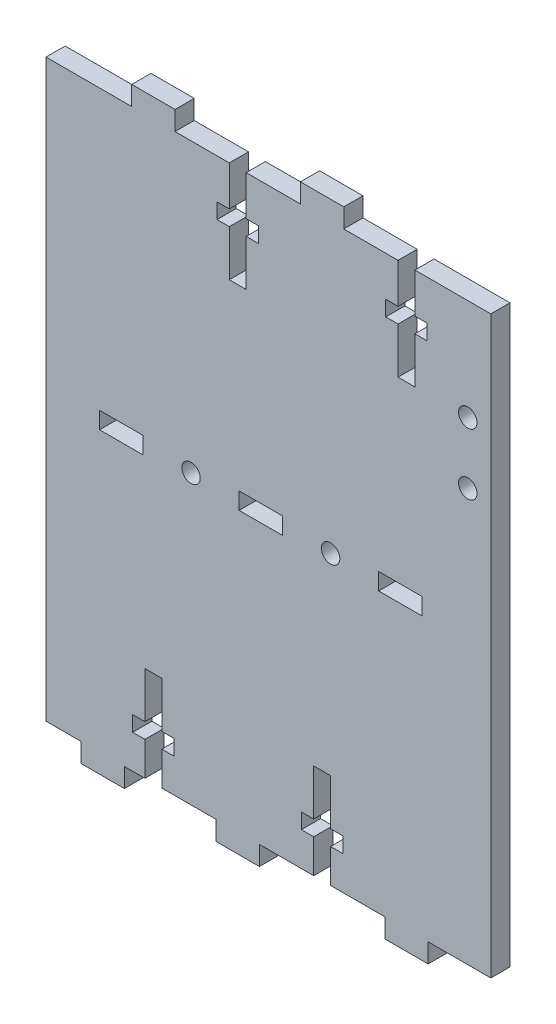
SolidWorks part; units mm, degrees
ref_plane "Front Plane" through (0, 0, 0) normal (0, 0, 1) x (1, 0, 0)
ref_plane "Top Plane" through (0, 0, 0) normal (0, 1, 0) x (1, 0, 0)
ref_plane "Right Plane" through (0, 0, 0) normal (1, 0, 0) x (0, 0, -1)
sketch "Sketch1" plane through (0, 0, 0) normal (0, 0, 1) x (1, 0, 0)
  line L0 (0, 0) -> (69.85, 0)
  line L1 (69.85, 0) -> (69.85, 95.25)
  line L2 (69.85, 95.25) -> (0, 95.25)
  line L3 (0, 95.25) -> (0, 0)
  line L4 (34.925, 95.25) -> (34.925, 0) construction
  line L5 (0, 47.625) -> (69.85, 47.625) construction
  line L6 (13.97, 0) -> (13.97, 15.748)
  line L7 (27.94, 95.25) -> (27.94, 78.486)
  line L8 (41.91, 0) -> (41.91, 15.748)
  line L9 (55.88, 95.25) -> (55.88, 78.486)
  line L10 (12.573, 15.748) -> (15.367, 15.748)
  line L11 (15.367, 15.748) -> (15.367, 8.128)
  line L12 (15.367, 8.128) -> (17.399, 8.128)
  line L13 (17.399, 8.128) -> (17.399, 5.588)
  line L14 (17.399, 5.588) -> (15.367, 5.588)
  line L15 (15.367, 5.588) -> (15.367, 0)
  line L16 (12.573, 5.588) -> (12.573, 0)
  line L17 (10.541, 5.588) -> (12.573, 5.588)
  line L18 (10.541, 8.128) -> (10.541, 5.588)
  line L19 (12.573, 8.128) -> (10.541, 8.128)
  line L20 (12.573, 15.748) -> (12.573, 8.128)
  line L21 (45.339, 5.588) -> (43.307, 5.588)
  line L22 (45.339, 8.128) -> (45.339, 5.588)
  line L23 (43.307, 8.128) -> (45.339, 8.128)
  line L24 (43.307, 15.748) -> (43.307, 8.128)
  line L25 (43.307, 15.748) -> (40.513, 15.748)
  line L26 (40.513, 15.748) -> (40.513, 8.128)
  line L27 (40.513, 8.128) -> (38.481, 8.128)
  line L28 (38.481, 8.128) -> (38.481, 5.588)
  line L29 (38.481, 5.588) -> (40.513, 5.588)
  line L30 (40.513, 5.588) -> (40.513, 0)
  line L31 (43.307, 5.588) -> (43.307, 0)
  line L32 (26.543, 78.486) -> (29.337, 78.486)
  line L33 (29.337, 78.486) -> (29.337, 86.106)
  line L34 (29.337, 86.106) -> (31.369, 86.106)
  line L35 (31.369, 86.106) -> (31.369, 88.646)
  line L36 (31.369, 88.646) -> (29.337, 88.646)
  line L37 (29.337, 88.646) -> (29.337, 95.25)
  line L38 (26.543, 88.646) -> (26.543, 95.25)
  line L39 (24.511, 88.646) -> (26.543, 88.646)
  line L40 (24.511, 86.106) -> (24.511, 88.646)
  line L41 (26.543, 86.106) -> (24.511, 86.106)
  line L42 (26.543, 78.486) -> (26.543, 86.106)
  line L43 (54.483, 88.646) -> (54.483, 95.25)
  line L44 (52.451, 88.646) -> (54.483, 88.646)
  line L45 (52.451, 86.106) -> (52.451, 88.646)
  line L46 (54.483, 86.106) -> (52.451, 86.106)
  line L47 (54.483, 78.486) -> (54.483, 86.106)
  line L48 (57.277, 78.486) -> (54.483, 78.486)
  line L49 (57.277, 78.486) -> (57.277, 86.106)
  line L50 (57.277, 86.106) -> (59.309, 86.106)
  line L51 (59.309, 86.106) -> (59.309, 88.646)
  line L52 (59.309, 88.646) -> (57.277, 88.646)
  line L53 (57.277, 88.646) -> (57.277, 95.25)
  line L54 (2.0002, 0) -> (2.0002, -3.175)
  line L55 (2.0002, -3.175) -> (9.1757, -3.175)
  line L56 (9.1757, -3.175) -> (9.1757, 0)
  line L57 (5.588, -3.175) -> (5.588, 0)
  line L58 (13.97, 95.25) -> (13.97, 98.425)
  line L59 (10.3823, 98.425) -> (17.5578, 98.425)
  line L60 (17.5578, 98.425) -> (17.5578, 95.25)
  line L61 (10.3823, 98.425) -> (10.3823, 95.25)
  line L62 (38.3222, 98.425) -> (38.3222, 95.25)
  line L63 (45.4977, 98.425) -> (38.3222, 98.425)
  line L64 (45.4977, 98.425) -> (45.4977, 95.25)
  line L65 (27.94, 0) -> (27.94, -3.175)
  line L66 (24.3523, -3.175) -> (31.5278, -3.175)
  line L67 (31.5278, -3.175) -> (31.5278, 0)
  line L68 (24.3523, -3.175) -> (24.3523, 0)
  line L69 (52.2923, -3.175) -> (52.2923, 0)
  line L70 (59.4678, -3.175) -> (52.2923, -3.175)
  line L71 (59.4678, -3.175) -> (59.4678, 0)
  line L73 (0, 95.25) -> (-3.81, 95.25)
  line L74 (0, 95.25) -> (0, 0)
  line L75 (0, 0) -> (-3.81, 0)
  line L76 (-3.81, 95.25) -> (-3.81, 0)
  dimension "D1" = 69.85
  dimension "D2" = 95.25
  dimension "D3" = 13.97
  dimension "D4" = 27.94
  dimension "D5" = 15.748
  dimension "D6" = 15.748
  dimension "D7" = 13.97
  dimension "D8" = 16.764
  dimension "D9" = 13.97
  dimension "D10" = 1.397
  dimension "D11" = 6.858
  dimension "D12" = 2.54
  dimension "D13" = 1.397
  dimension "D14" = 1.397
  dimension "D15" = 7.62
  dimension "D16" = 2.54
  dimension "D17" = 6.858
  dimension "D18" = 2.794
  dimension "D19" = 7.62
  dimension "D20" = 16.764
  dimension "D21" = 5.588
  dimension "D22" = 3.175
  dimension "D23" = 7.1755
  dimension "D24" = 3.175
  dimension "D25" = 3.5877
  dimension "D26" = 3.5877
  dimension "D27" = 3.175
  dimension "D28" = 3.81
  dimension "D29" = 6.604
  dimension "D30" = 2.032
  dimension "D31" = 3.81
extrude "Boss-Extrude1" add sketch "Sketch1" along normal blind 3.175 contours L53 L52 L51 L50 L49 L48 L47 L46 L45 L44 L43 L2 L37 L36 L35 L34 L33 L32 L42 L41 L40 L39 L38 L3 L0 L16 L17 L18 L19 L20 L10 L11 L12 L13 L14 L15 | L59 L61 L2 L58 | L60 L59 L58 L2 | L64 L63 L62 L2 | L70 L71 L0 L69 | L57 L55 L56 L0 | L55 L57 L0 L54 | L68 L66 L65 L0 | L66 L67 L0 L65 | L73 L76 L75 L3
sketch "Sketch4" plane through (0, 0, 3.175) normal (0, 0, 1) x (1, 0, 0)
  line L0 (66.04, 68.326) -> (66.04, 78.486)
  line L1 (69.85, 0) -> (69.85, 95.25) construction
  line L3 (69.85, 69.85) -> (69.85, 0)
  line L8 (69.85, 59.69) -> (69.85, 0)
  circle A4 centre (66.04, 68.326) radius 1.524
  circle A5 centre (66.04, 78.486) radius 1.524
  dimension "D2" = 10.16
extrude "Cut-Extrude1" cut sketch "Sketch4" against normal through all
sketch "Sketch5" plane through (0, 0, 3.175) normal (0, 0, 1) x (1, 0, 0)
  line L0 (-3.81, 0) -> (-3.81, 47.625)
  line L1 (-3.81, 95.25) -> (-3.81, 0) construction
  line L2 (-3.81, 47.625) -> (5.0615, 47.625)
  line L3 (5.0615, 47.625) -> (5.0615, 49.022)
  line L4 (5.0615, 47.625) -> (5.0615, 46.228)
  line L5 (5.0615, 46.228) -> (12.237, 46.228)
  line L6 (12.237, 46.228) -> (12.237, 49.022)
  line L7 (12.237, 49.022) -> (5.0615, 49.022)
  line L8 (12.237, 47.625) -> (20.2063, 47.625)
  line L9 (20.2063, 47.625) -> (28.1755, 47.625)
  line L10 (28.1755, 47.625) -> (28.1755, 49.022)
  line L11 (28.1755, 49.022) -> (35.351, 49.022)
  line L12 (35.351, 49.022) -> (35.351, 46.228)
  line L13 (35.351, 46.228) -> (28.1755, 46.228)
  line L14 (28.1755, 46.228) -> (28.1755, 47.625)
  line L15 (28.1755, 46.228) -> (28.1755, 47.625)
  line L16 (35.351, 47.625) -> (43.3203, 47.625)
  line L17 (43.3203, 47.625) -> (51.2895, 47.625)
  line L18 (51.2895, 47.625) -> (51.2895, 49.022)
  line L19 (51.2895, 49.022) -> (58.465, 49.022)
  line L20 (58.465, 49.022) -> (58.465, 46.228)
  line L21 (58.465, 46.228) -> (51.2895, 46.228)
  line L22 (51.2895, 46.228) -> (51.2895, 47.625)
  circle A0 centre (20.2063, 47.625) radius 1.524
  circle A1 centre (43.3203, 47.625) radius 1.524
  dimension "D6" = 7.9692
  dimension "D10" = 7.9692
  dimension "D1" = 8.8715
  dimension "D2" = 1.397
  dimension "D3" = 1.397
  dimension "D4" = 7.1755
  dimension "D5" = 7.9692
  dimension "D7" = 7.1755
  dimension "D8" = 2.794
  dimension "D9" = 7.9692
  dimension "D11" = 2.794
  dimension "D12" = 7.1755
extrude "Cut-Extrude2" cut sketch "Sketch5" against normal through all contours L6 L7 L3 L4 L5 | L8 A0 L9 | L9 A0 L8 | L14 L13 L12 L11 L10 | L17 A1 L16 | L16 A1 L17 | L22 L21 L20 L19 L18
